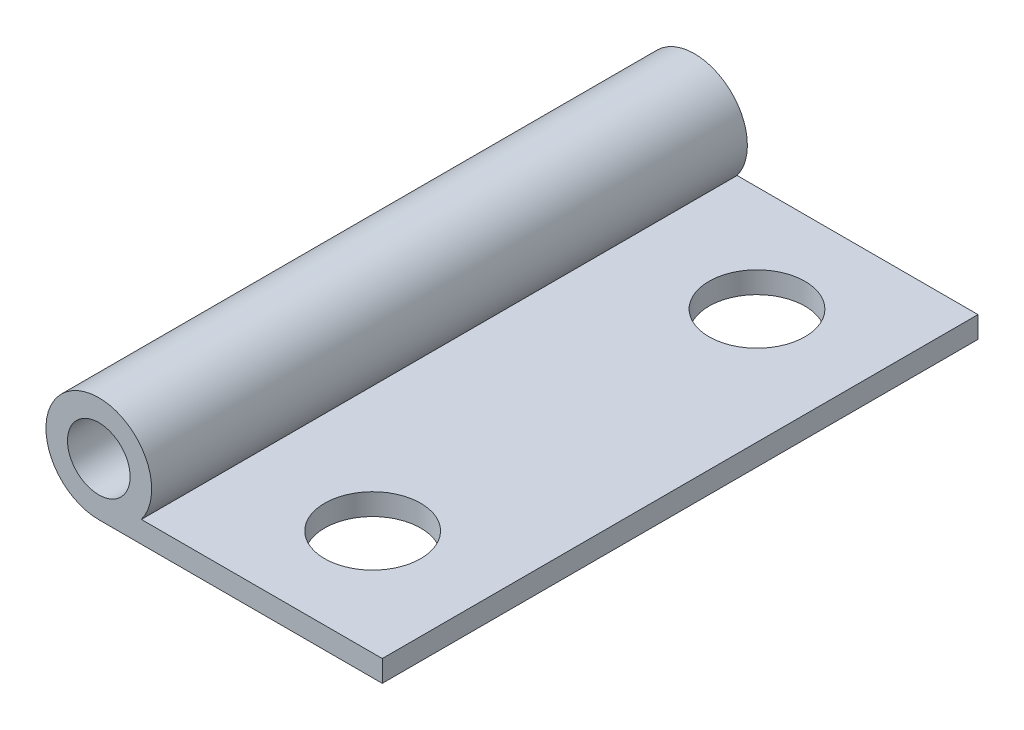
SolidWorks part; units mm, degrees
ref_plane "Front Plane" through (0, 0, 0) normal (0, 0, 1) x (1, 0, 0)
ref_plane "Top Plane" through (0, 0, 0) normal (0, 1, 0) x (1, 0, 0)
ref_plane "Right Plane" through (0, 0, 0) normal (1, 0, 0) x (0, 0, -1)
sketch "Sketch1" plane through (0, 0, 0) normal (0, 1, 0) x (1, 0, 0)
  line L0 (0, 10) -> (0, -10) construction
  line L1 (-6, 15.5) -> (6, 15.5)
  line L2 (-6, 15.5) -> (-6, -15.5)
  line L3 (-6, -15.5) -> (6, -15.5)
  line L4 (6, 15.5) -> (6, -15.5)
  line L5 (-6, 15.5) -> (6, -15.5) construction
  line L6 (-6, -15.5) -> (6, 15.5) construction
  circle A0 centre (0, 10) radius 2.5
  circle A1 centre (0, -10) radius 2.5
  point P0 (0, 0)
  point P10 (0, 0)
  dimension "D3" = 5
  dimension "D4" = 5
  dimension "D1" = 31
  dimension "D2" = 12
  dimension "D5" = 5.5
extrude "Boss-Extrude1" add sketch "Sketch1" along normal blind 1.12
sketch "Sketch2" plane through (0, 0, 15.5) normal (0, 0, 1) x (1, 0, 0)
  line L0 (-6, 0) -> (6, 0) construction
  line L1 (-6, 1.12) -> (-6, 0) construction
  line L3 (-6, 1.12) -> (-6.5351, 1.12)
  line L4 (-6, 1.12) -> (-6, 0)
  line L5 (-6, 0) -> (-8.75, 0)
  arc A0 (-6.5351, 1.12) -> (-8.75, 0) centre (-8.75, 2.75) ccw
  circle A1 centre (-8.75, 2.75) radius 1.63
  dimension "D1" = 2.75
  dimension "D2" = 3.26
extrude "Boss-Extrude2" add sketch "Sketch2" against normal up to surface (31 mm away) up to face at (0, 0.56, -15.5)
